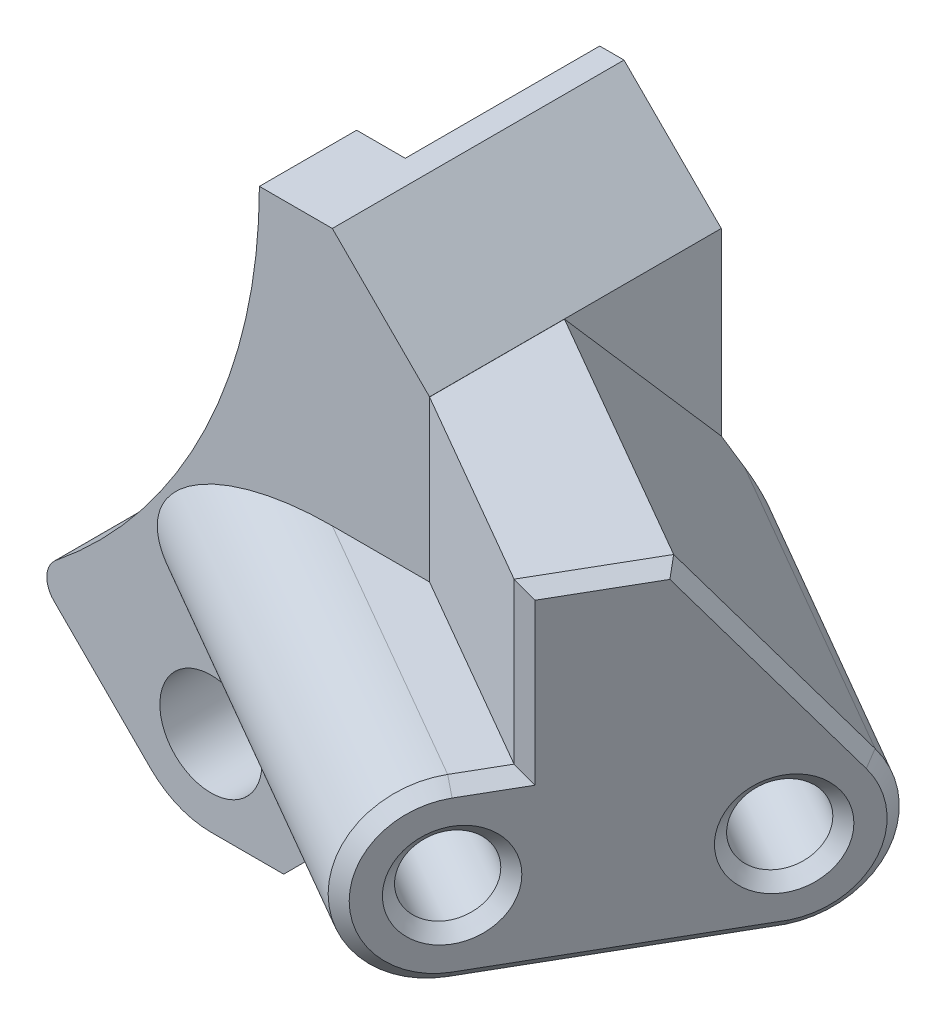
SolidWorks part; units mm, degrees
ref_plane "Front Plane" through (0, 0, 0) normal (0, 0, 1) x (1, 0, 0)
ref_plane "Top Plane" through (0, 0, 0) normal (0, 1, 0) x (1, 0, 0)
ref_plane "Right Plane" through (0, 0, 0) normal (1, 0, 0) x (0, 0, -1)
sketch "Sketch1" plane through (0, 0, 0) normal (0, 0, 1) x (1, 0, 0)
  line L0 (-20.5061, 20.5061) -> (20.5061, -20.5061) construction
  line L1 (-24.5, 0) -> (24.5, 0) construction
  line L5 (13.2414, -18.1911) -> (18.0312, -22.981)
  line L8 (29.5, -24.0061) -> (29.5, 0)
  line L9 (29.5, -24.0061) -> (20.5061, -24.0061)
  line L10 (29.5, 0) -> (22.5, 0)
  circle A0 centre (0, 0) radius 24.5 construction
  circle A2 centre (20.5061, -20.5061) radius 2.1
  arc A4 (18.0312, -22.981) -> (20.5061, -24.0061) centre (20.5061, -20.5061) ccw
  arc A7 (13.2414, -18.1911) -> (22.5, 0) centre (0, 0) ccw
  point P20 (0, -24.5)
  dimension "D1" = 4.2
  dimension "D3" = 49
  dimension "D5" = 2
  dimension "D6" = 54
  dimension "D7" = 3.5
  dimension "D2" = 58
  dimension "D4" = 45
extrude "Boss-Extrude1" add sketch "Sketch1" along normal blind 12
sketch "Sketch2" plane through (0, -24.0061, 0) normal (0, -1, 0) x (1, 0, 0)
  line L0 (29.5, 12) -> (36.4282, 0) construction
  line L1 (36.4282, 0) -> (29.5, 0)
  line L2 (29.5, 0) -> (29.5, 12)
  line L3 (29.5, 12) -> (38.1603, 17)
  line L4 (38.1603, 17) -> (45.0885, 5)
  line L5 (45.0885, 5) -> (36.4282, 0)
  dimension "D1" = 30
  dimension "D2" = 10
extrude "Boss-Extrude2" add sketch "Sketch2" against normal blind 13.79 from offset 6.21 offset against normal yes
sketch "Sketch3" plane through (0, 0, 0) normal (0, 0, -1) x (-1, 0, 0)
  line L0 (-18.0312, -22.981) -> (-14.6716, -19.6213)
  line L1 (-13.2414, -18.1911) -> (-18.0312, -22.981) construction
  line L2 (-22.981, -18.0312) -> (-19.6213, -14.6716)
  line L3 (-24.0061, -20.5061) -> (-24.0061, -24.0061)
  line L4 (-20.5061, -24.0061) -> (-29.5, -24.0061) construction
  line L5 (-24.0061, -24.0061) -> (-20.5061, -24.0061)
  arc A0 (-14.6716, -19.6213) -> (-19.6213, -14.6716) centre (0, 0) ccw
  arc A1 (-22.5, 0) -> (-13.2414, -18.1911) centre (0, 0) ccw construction
  arc A2 (-22.981, -18.0312) -> (-24.0061, -20.5061) centre (-20.5061, -20.5061) ccw
  arc A3 (-20.5061, -24.0061) -> (-18.0312, -22.981) centre (-20.5061, -20.5061) ccw construction
  arc A4 (-20.5061, -24.0061) -> (-18.0312, -22.981) centre (-20.5061, -20.5061) ccw
  dimension "D1" = 2
extrude "Cut-Extrude1" cut sketch "Sketch3" against normal offset from surface (8 mm away) 4 up to face at (24.2948, -13.8195, 12)
sketch "Sketch5" plane through (35.9814, 0, 20.7739) normal (0.866, 0, 0.5) x (0.5, 0, -0.866)
  line L0 (2.3577, -10.5961) -> (4.3577, -10.5961)
  line L1 (4.3577, -4.0061) -> (4.3577, -17.7961) construction
  line L2 (4.3577, -10.5961) -> (4.3577, -17.7961)
  line L3 (4.3577, -17.7961) -> (2.3577, -17.7961)
  line L4 (4.3577, -24.0061) -> (4.3577, -17.7961) construction
  line L5 (18.2141, -17.7961) -> (4.3577, -17.7961) construction
  arc A0 (2.3577, -10.5961) -> (2.3577, -17.7961) centre (2.3577, -14.1961) ccw
  dimension "D1" = 3.6
  dimension "D2" = 2
extrude "Boss-Extrude3" add sketch "Sketch5" against normal up to surface (10 mm away)
sketch "Sketch4" plane through (35.9814, 0, 20.7739) normal (0.866, 0, 0.5) x (0.5, 0, -0.866)
  line L0 (4.3577, -4.0061) -> (4.3577, -10.5961) construction
  circle A0 centre (2.3577, -14.2) radius 1.6
  circle A1 centre (12.3577, -14.2) radius 1.6
  dimension "D4" = 3.2
  dimension "D1" = 10
  dimension "D2" = 14.2
  dimension "D3" = 8
extrude "Cut-Extrude2" cut sketch "Sketch4" against normal through all
chamfer "Chamfer2" distance 4 angle 45 1 edges at (29.5, 0, 6)
sketch "Sketch7" plane through (35.9814, 0, 20.7739) normal (0.866, 0, 0.5) x (0.5, 0, -0.866)
  line L0 (15.2294, -12.029) -> (9.1639, -4.0061)
  line L3 (18.2141, -17.7961) -> (2.3577, -17.7961) construction
  line L4 (4.3577, -4.0061) -> (14.75, -4.0061) construction
  line L6 (22.0419, -24.0061) -> (22.0419, -4.0061)
  line L7 (22.0419, -4.0061) -> (9.1639, -4.0061)
  line L8 (12.3577, -17.8) -> (2.3577, -17.7961)
  line L9 (2.3577, -17.7961) -> (2.3577, -24.0061)
  line L10 (-0.1393, -24.0061) -> (4.3577, -24.0061) construction
  line L11 (2.3577, -24.0061) -> (22.0419, -24.0061)
  arc A0 (12.3577, -17.8) -> (15.2294, -12.029) centre (12.3577, -14.2) ccw
  arc A1 (2.3577, -10.5961) -> (2.3577, -17.7961) centre (2.3577, -14.1961) ccw construction
  arc A2 (2.3577, -10.5961) -> (2.3577, -17.7961) centre (2.3577, -14.1961) ccw construction
  dimension "D2" = 7.2
  dimension "D1" = 127.09
extrude "Cut-Extrude3" cut sketch "Sketch7" against normal up to surface (14.6188 mm away)
chamfer "Chamfer3" distance 6 angle 45 1 edges at (29.5, -24.0061, 6)
sketch "Sketch8" plane through (35.9814, 0, 20.7739) normal (0.866, 0, 0.5) x (0.5, 0, -0.866)
  line L1 (5.2577, -15.8743) -> (5.2577, -12.5257)
  line L2 (5.2577, -12.5257) -> (2.3577, -10.8514)
  line L3 (2.3577, -10.8514) -> (-0.5423, -12.5257)
  line L4 (-0.5423, -12.5257) -> (-0.5423, -15.8743)
  line L5 (-0.5423, -15.8743) -> (2.3577, -17.5486)
  line L6 (2.3577, -17.5486) -> (5.2577, -15.8743)
  line L7 (9.4577, -12.5257) -> (9.4577, -15.8743)
  line L8 (9.4577, -15.8743) -> (12.3577, -17.5486)
  line L9 (12.3577, -17.5486) -> (15.2577, -15.8743)
  line L10 (15.2577, -15.8743) -> (15.2577, -12.5257)
  line L11 (15.2577, -12.5257) -> (12.3577, -10.8514)
  line L12 (12.3577, -10.8514) -> (9.4577, -12.5257)
  circle A0 centre (2.3577, -14.2) radius 2.9 construction
  circle A1 centre (12.3577, -14.2) radius 2.9 construction
  dimension "D1" = 5.8
extrude "Cut-Extrude4" cut sketch "Sketch8" against normal through all from offset 12.5 offset against normal yes
fillet "Fillet1" radius 1 2 edges at (13.2414, -18.1911, 10) (24.0061, -23.5, 4)
chamfer "Chamfer4" distance 0.5 angle 45 9 edges at (37.9603, -14.2, 17.3464) (42.9603, -14.2, 8.6862) (39.7022, -17.7961, 14.3294) (35.3603, -14.1961, 21.8497) (37.6603, -10.5961, 17.866) (38.1603, -7.3011, 17) (39.3618, -4.0061, 14.9188) (42.0797, -8.0175, 10.2113) (43.79, -15.7283, 7.249)
fillet "Fillet2" radius 3 1 edges at (19.6213, -14.6716, 2.8324)
